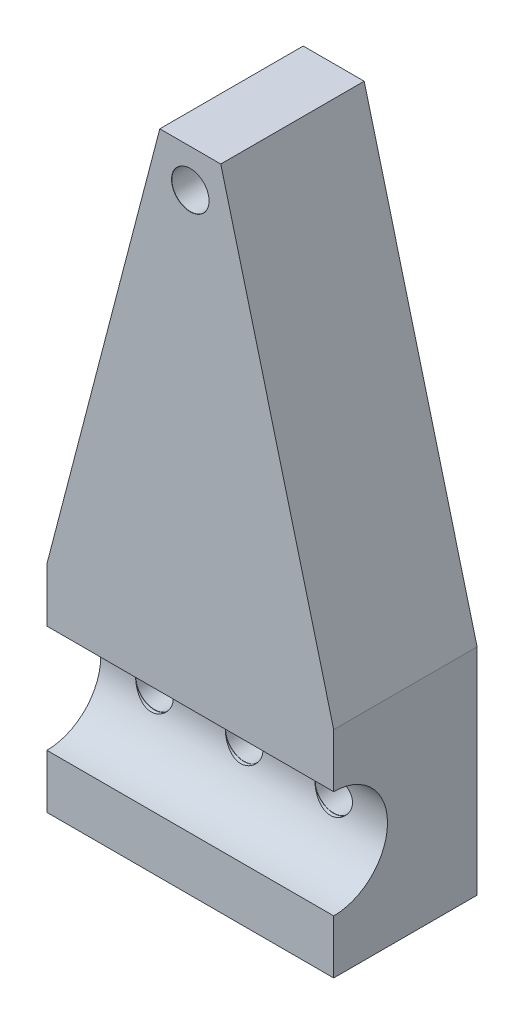
SolidWorks part; units mm, degrees
ref_plane "Front Plane" through (0, 0, 0) normal (0, 0, 1) x (1, 0, 0)
ref_plane "Top Plane" through (0, 0, 0) normal (0, 1, 0) x (1, 0, 0)
ref_plane "Right Plane" through (0, 0, 0) normal (1, 0, 0) x (0, 0, -1)
sketch "Sketch1" plane through (0, 0, 0) normal (0, 0, 1) x (1, 0, 0)
  line L0 (-25.4, 19.05) -> (-5.3997, 95.8011)
  line L1 (25.4, -19.05) -> (-25.4, -19.05)
  line L2 (25.4, -19.05) -> (25.4, 19.05)
  line L3 (25.4, 19.05) -> (-25.4, 19.05)
  line L4 (-25.4, -19.05) -> (-25.4, 19.05)
  line L5 (25.4, -19.05) -> (-25.4, 19.05) construction
  line L6 (25.4, 19.05) -> (-25.4, -19.05) construction
  line L7 (-5.3997, 95.8011) -> (5.3997, 95.8011)
  line L8 (5.3997, 95.8011) -> (25.4, 19.05)
  line L9 (-15.875, 0) -> (15.875, 0) construction
  line L10 (0, 95.8011) -> (0, 89.0924) construction
  point P0 (0, 0)
  point P8 (0, 95.8011)
  point P9 (0, 0)
  dimension "D1" = 50.8
  dimension "D2" = 38.1
  dimension "D4" = 31.75
extrude "Boss-Extrude1" add sketch "Sketch1" along normal blind 25.4 contours L8 L7 L0 L3 | L4 L1 L2 L3
sketch "Sketch2" plane through (0, 0, 25.4) normal (0, 0, 1) x (1, 0, 0)
  line L0 (-25.4, 0) -> (25.4, 0)
  line L1 (-25.4, -19.05) -> (-25.4, 19.05) construction
  line L2 (25.4, -19.05) -> (25.4, 19.05) construction
sweep "Cut-Sweep1" cut path "Sketch2" circular profile diameter 19.05 parameters "D3"=19.05
hole_wizard "M6 Clearance Hole1" positions "3DSketch1" profile "Sketch9" hole size "M6" standard "ANSI Metric" end condition through all
sketch3d "3DSketch1"
  point P0 (0, 0, 15.875)
  point P4 (-15.875, 0, 15.875)
  point P6 (15.875, 0, 15.875)
  point P8 (0, 89.0924, 25.4)
sketch "Sketch9" plane through (0, 0, 15.875) normal (1, 0, 0) x (0, -1, 0)
  line L0 (0, 0) -> (0, 15.875)
  line L1 (0, 15.875) -> (3.3, 15.875)
  line L2 (3.3, 15.875) -> (3.3, 0.025)
  line L3 (3.3, 0.025) -> (3.325, 0)
  line L5 (3.325, 0) -> (0, 0)
  line L6 (-3.3, 0.025) -> (-3.325, 0) construction
  line L11 (0, -6.35) -> (0, 107.95) construction
  dimension "Thru Hole Dia." = 6.6
  dimension "Thru Hole Depth" = 15.875
  dimension "Near C'Sink Dia." = 6.65
  dimension "Near C'Sink Angle" = 90
equation "\"Rover_Length\"= 25in"
equation "\"Rover_Width\"= 18in"
equation "\"Rover_Height\"= 12in"
equation "\"Chassis_Wheelbase\"= 28in"
equation "\"Chassis_WheelDiam\"= 171mm"
equation "\"Chassis_ArmDiamWidth\"= 0.75in"
equation "\"Chassis_ArmAngle\"= 135deg"
equation "\"Chassis_ArmHeight\"= 8in"
equation "\"Chassis_HubMountOD\"= 3in"
equation "\"Chassis_WheelBoltHole\"= 36mm"
equation "\"Chassis_WheelBoltNum\"= 4"
equation "\"Chassis_DiffBarLength\"= 12in"
equation "\"Chassis_DiffBarWidth\"= 1in"
equation "\"Chassis_DiffBarHeight\"= 0.5in"
equation "\"Chassis_DiffLinkage_Length\"= 2.5in"
equation "\"Chassis_MountBracketThickness\"= 0.125in"
equation "\"Chassis_MountBracketWidth\"= 3in"
equation "\"Chassis_MountBacketOverlap\"= 0.5in"
equation "\"Chassis_ArmShaftDiam\"= 0.75in"
equation "\"Chassis_ArmHoleSpacing\" = 1.25in"
equation "\"D4@Sketch1\"=\"Chassis_ArmHoleSpacing\""
